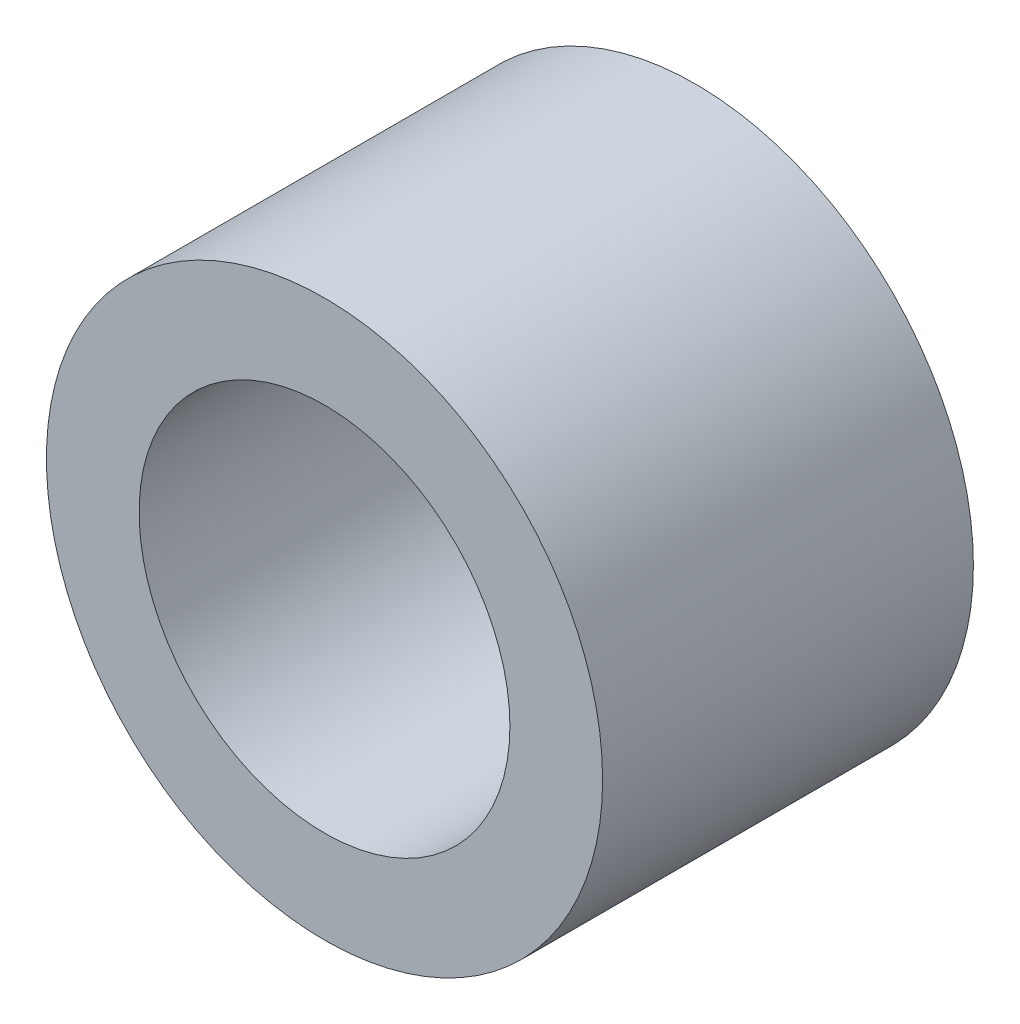
SolidWorks part; units mm, degrees
ref_plane "Front Plane" through (0, 0, 0) normal (0, 0, 1) x (1, 0, 0)
ref_plane "Top Plane" through (0, 0, 0) normal (0, 1, 0) x (1, 0, 0)
ref_plane "Right Plane" through (0, 0, 0) normal (1, 0, 0) x (0, 0, -1)
sketch "Sketch1" plane through (0, 0, 0) normal (0, 0, 1) x (1, 0, 0)
  circle A0 centre (0, 0) radius 4.7625
  circle A1 centre (0, 0) radius 3.175
  dimension "D1" = 9.525
  dimension "ID" = 6.35
extrude "Extrude1" add sketch "Sketch1" along normal mid plane 6.35
sketch "Sketch2" plane through (0, 0, 0) normal (1, 0, 0) x (0, 0, -1)
  line L0 (-3.175, -3.175) -> (3.175, -3.175) construction
  line L3 (3.175, 3.175) -> (-3.175, 3.175) construction
  line L5 (-3.175, -3.175) -> (3.175, -3.175)
  line L6 (3.175, 3.175) -> (-3.175, 3.175)
sketch "Sketch4" plane through (0, 0, 3.175) normal (0, 0, 1) x (1, 0, 0)
  line L0 (0, 0) -> (-2.2451, 2.2451)
  line L1 (0, -3.4925) -> (0, 3.4925) construction
  circle A0 centre (0, 0) radius 3.175 construction
  dimension "D1" = 45
